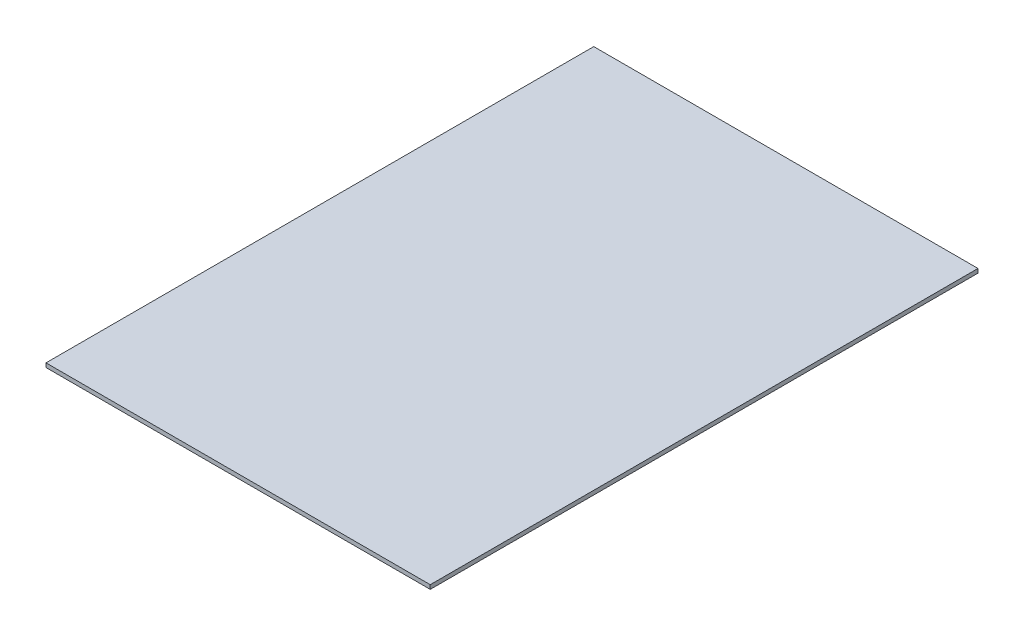
SolidWorks part; units mm, degrees
material "Acrylic (Medium-high impact)"
ref_plane "Front Plane" through (0, 0, 0) normal (0, 0, 1) x (1, 0, 0)
ref_plane "Top Plane" through (0, 0, 0) normal (0, 1, 0) x (1, 0, 0)
ref_plane "Right Plane" through (0, 0, 0) normal (1, 0, 0) x (0, 0, -1)
sketch "Sketch1" plane through (0, 0, 0) normal (0, 1, 0) x (1, 0, 0)
  line L1 (0, 0) -> (-470, 0)
  line L2 (0, 0) -> (0, 670)
  line L3 (0, 670) -> (-470, 670)
  line L4 (-470, 0) -> (-470, 670)
  line L5 (0, 0) -> (-470, 670) construction
  line L6 (0, 670) -> (-470, 0) construction
  point P4 (-235, 335)
  dimension "D1" = 470
  dimension "D2" = 670
extrude "Boss-Extrude1" add sketch "Sketch1" along normal blind 5
